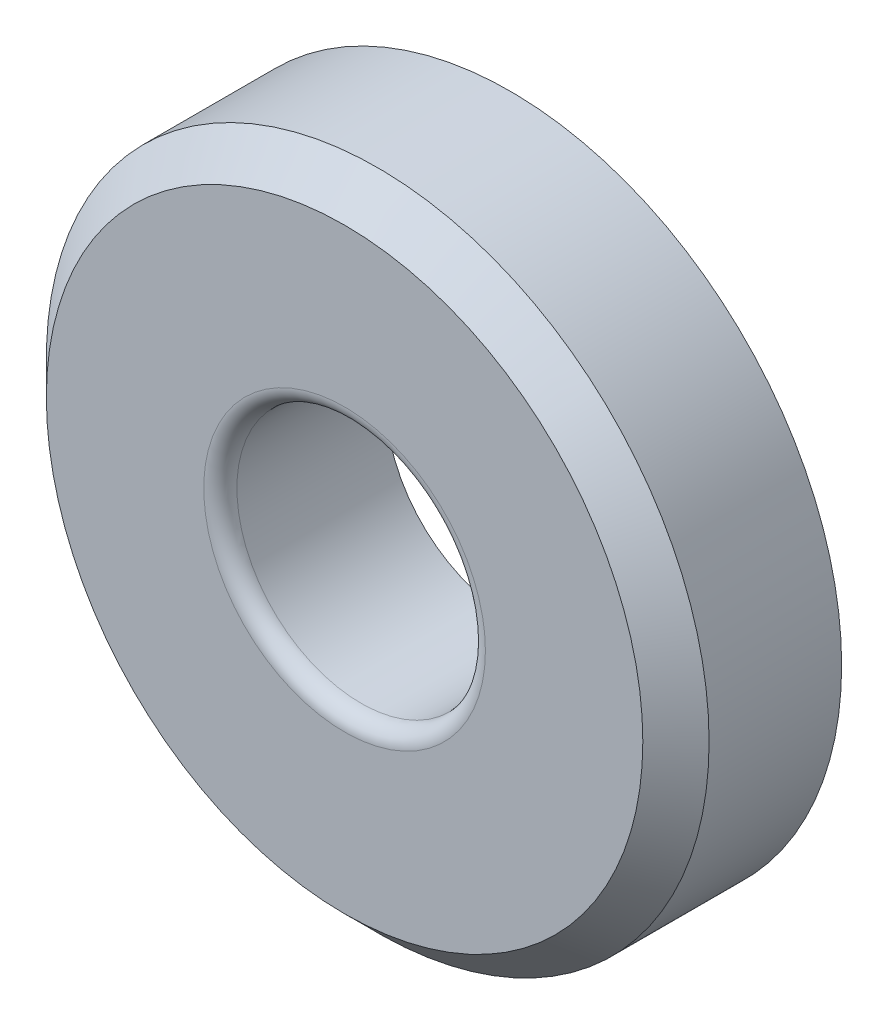
SolidWorks part; units mm, degrees
ref_plane "Ön Düzlem" through (0, 0, 0) normal (0, 0, 1) x (1, 0, 0)
ref_plane "Üst Düzlem" through (0, 0, 0) normal (0, 1, 0) x (1, 0, 0)
ref_plane "Sağ Düzlem" through (0, 0, 0) normal (1, 0, 0) x (0, 0, -1)
sketch "Çizim1" plane through (0, 0, 0) normal (0, 0, 1) x (1, 0, 0)
  circle A0 centre (0, 0) radius 25.4
  circle A1 centre (0, 0) radius 9.525
  dimension "D1" = 19.05
  dimension "D2" = 50.8
extrude "Yükseklik-Ekstrüzyon1" add sketch "Çizim1" along normal blind 12.7
chamfer "Pah1" distance 2.54 angle 45 1 edges at (25.4, 0, 12.7)
fillet "Radyus1" radius 1.27 1 edges at (9.525, 0, 12.7)
